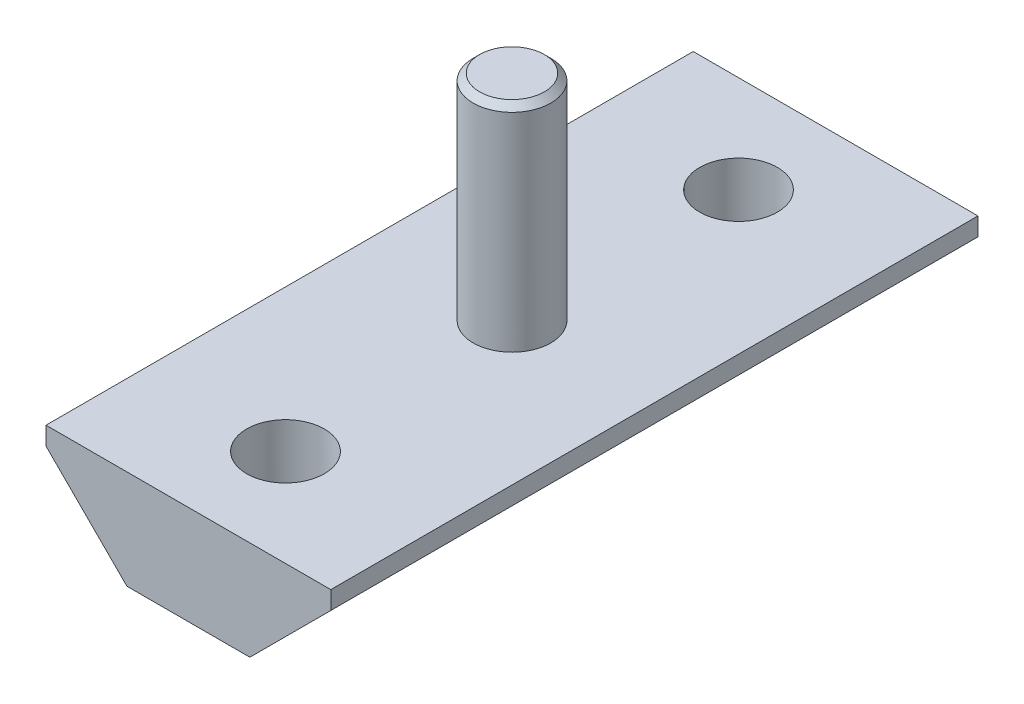
SolidWorks part; units mm, degrees
ref_plane "Ebene vorne" through (0, 0, 0) normal (0, 0, 1) x (1, 0, 0)
ref_plane "Ebene oben" through (0, 0, 0) normal (0, 1, 0) x (1, 0, 0)
ref_plane "Ebene rechts" through (0, 0, 0) normal (1, 0, 0) x (0, 0, -1)
sketch "Sketch1" plane through (0, 0, 0) normal (0, 0, 1) x (1, 0, 0)
  line L0 (0, 42.9987) -> (0, -29.6613) construction
  line L1 (11, 7.65) -> (-11, 7.65)
  line L2 (-11, 7.65) -> (-11, 6.25)
  line L3 (-11, 6.25) -> (-4.75, 0)
  line L4 (-4.75, 0) -> (4.75, 0)
  line L5 (11, 6.25) -> (4.75, 0)
  line L6 (11, 7.65) -> (11, 6.25)
  point P10 (0, 0)
  point P12 (0, 7.65)
  dimension "D1" = 7.65
  dimension "D2" = 11
  dimension "D3" = 1.4
  dimension "D4" = 4.75
extrude "Boss-Extrude1" add sketch "Sketch1" along normal mid plane 50
sketch "Sketch2" plane through (0, 7.65, 0) normal (0, 1, 0) x (1, 0, 0)
  circle A0 centre (0, 0) radius 3
  dimension "D1" = 6
extrude "Boss-Extrude2" add sketch "Sketch2" along normal blind 16.55
sketch "Sketch3" plane through (0, 7.65, 0) normal (0, 1, 0) x (1, 0, 0)
  line L0 (-11, 0) -> (11, 0) construction
  line L1 (-11, -25) -> (-11, 25) construction
  line L2 (11, -25) -> (11, 25) construction
  circle A0 centre (0, 17.5) radius 3
  circle A1 centre (0, -17.5) radius 3
  dimension "D1" = 6
  dimension "D2" = 17.5
  dimension "D3" = 11
extrude "Cut-Extrude1" cut sketch "Sketch3" against normal blind 10
chamfer "Chamfer1" distance 0.5 angle 45 1 edges at (0, 24.2, 3)
